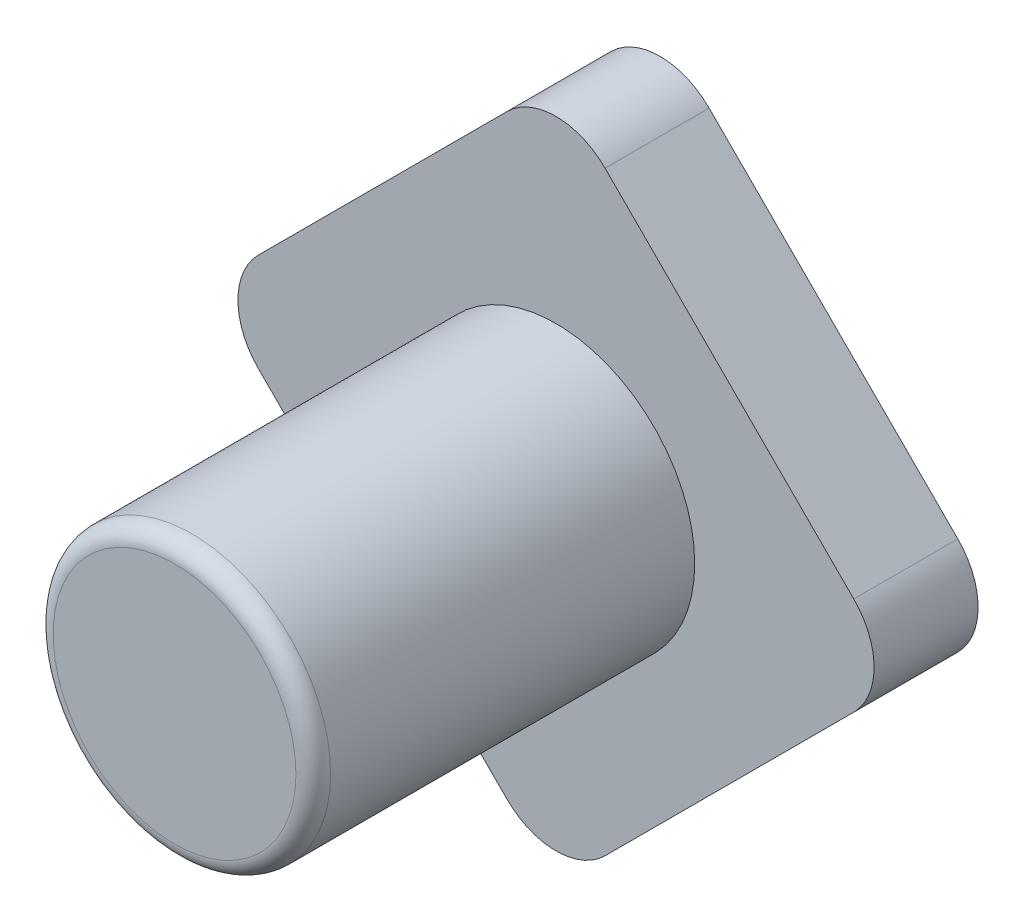
SolidWorks part; units mm, degrees
ref_plane "Front Plane" through (0, 0, 0) normal (0, 0, 1) x (1, 0, 0)
ref_plane "Top Plane" through (0, 0, 0) normal (0, 1, 0) x (1, 0, 0)
ref_plane "Right Plane" through (0, 0, 0) normal (1, 0, 0) x (0, 0, -1)
sketch "Sketch1" plane through (0, 0, 0) normal (0, 0, 1) x (1, 0, 0)
  line L0 (0, 10) -> (10, 0)
  line L5 (10, 0) -> (0, -10)
  line L6 (0, -10) -> (-10, 0)
  line L7 (-10, 0) -> (0, 10)
  dimension "D1" = 10
  dimension "D2" = 10
  dimension "D3" = 10
  dimension "D4" = 10
extrude "Boss-Extrude1" add sketch "Sketch1" against normal blind 3
sketch "Sketch2" plane through (0, 0, 0) normal (0, 0, 1) x (1, 0, 0)
  circle A0 centre (0, 0) radius 4
  dimension "D1" = 8
extrude "Boss-Extrude2" add sketch "Sketch2" along normal blind 11
fillet "Fillet1" radius 2 4 edges at (0, -10, -1.5) (10, 0, -1.5) (-10, 0, -1.5) (0, 10, -1.5)
fillet "Fillet2" radius 0.5 1 edges at (4, 0, 11)
